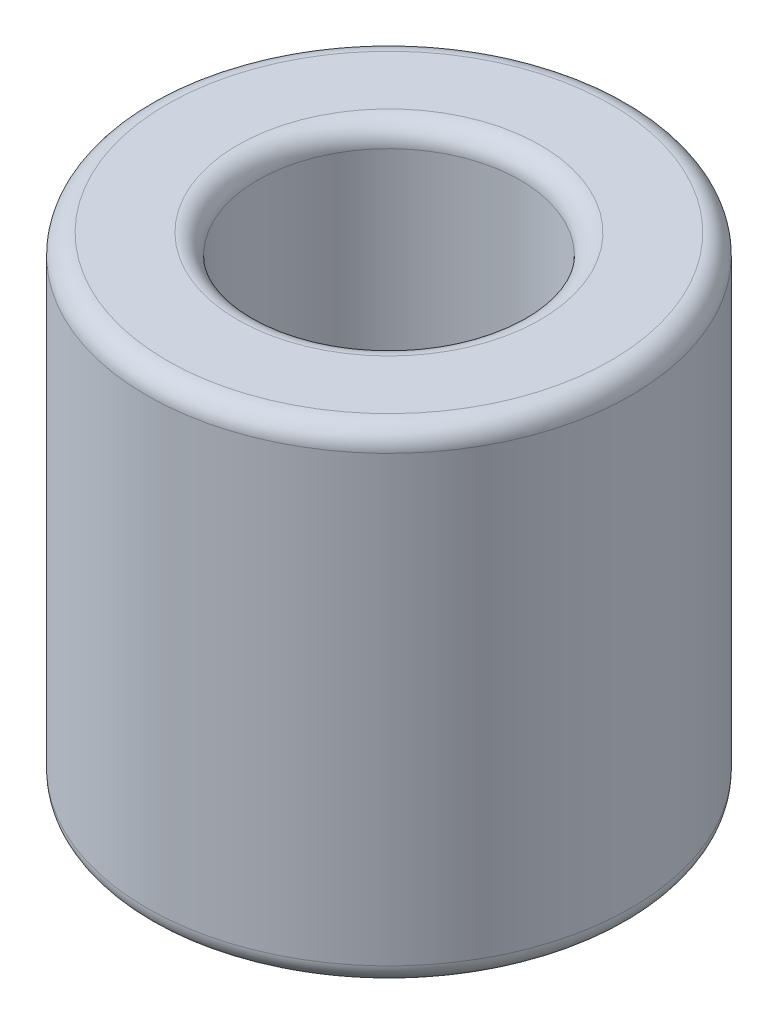
SolidWorks part; units mm, degrees
ref_plane "Front Plane" through (0, 0, 0) normal (0, 0, 1) x (1, 0, 0)
ref_plane "Top Plane" through (0, 0, 0) normal (0, 1, 0) x (1, 0, 0)
ref_plane "Right Plane" through (0, 0, 0) normal (1, 0, 0) x (0, 0, -1)
sketch "Sketch1" plane through (0, 0, 0) normal (0, 1, 0) x (1, 0, 0)
  circle A0 centre (0, 0) radius 3
  circle A1 centre (0, 0) radius 1.625
  dimension "D1" = 6
  dimension "D2" = 3.25
extrude "Boss-Extrude1" add sketch "Sketch1" along normal blind 6
fillet "Fillet1" radius 0.25 4 edges at (0, 6, 1.625) (0, 6, 3) (0, 0, 1.625) (0, 0, 3)
